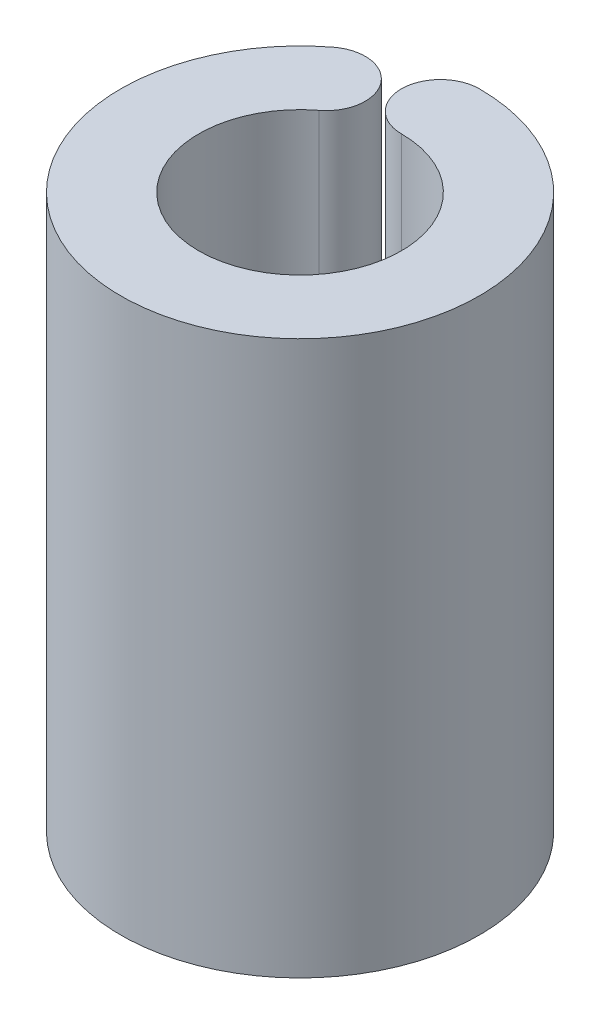
SolidWorks part; units mm, degrees
ref_plane "Front Plane" through (0, 0, 0) normal (0, 0, 1) x (1, 0, 0)
ref_plane "Top Plane" through (0, 0, 0) normal (0, 1, 0) x (1, 0, 0)
ref_plane "Right Plane" through (0, 0, 0) normal (1, 0, 0) x (0, 0, -1)
sketch "Sketch1" plane through (0, 0, 0) normal (0, 1, 0) x (1, 0, 0)
  arc A0 (0, 3.6) -> (-2.1873, 2.8593) centre (0, 0) cw
  arc A1 (0, 2.6) -> (-1.5798, 2.065) centre (0, 0) cw
  arc A2 (0, 4.6) -> (-2.7949, 3.6535) centre (0, 0) cw
  arc A3 (0, 2.6) -> (0, 4.6) centre (0, 3.6) cw
  arc A4 (-1.5798, 2.065) -> (-2.7949, 3.6535) centre (-2.1873, 2.8593) ccw
  dimension "D1" = 3.6
  dimension "D2" = 1
  dimension "D3" = 1
extrude "Boss-Extrude1" add sketch "Sketch1" along normal blind 14.2
